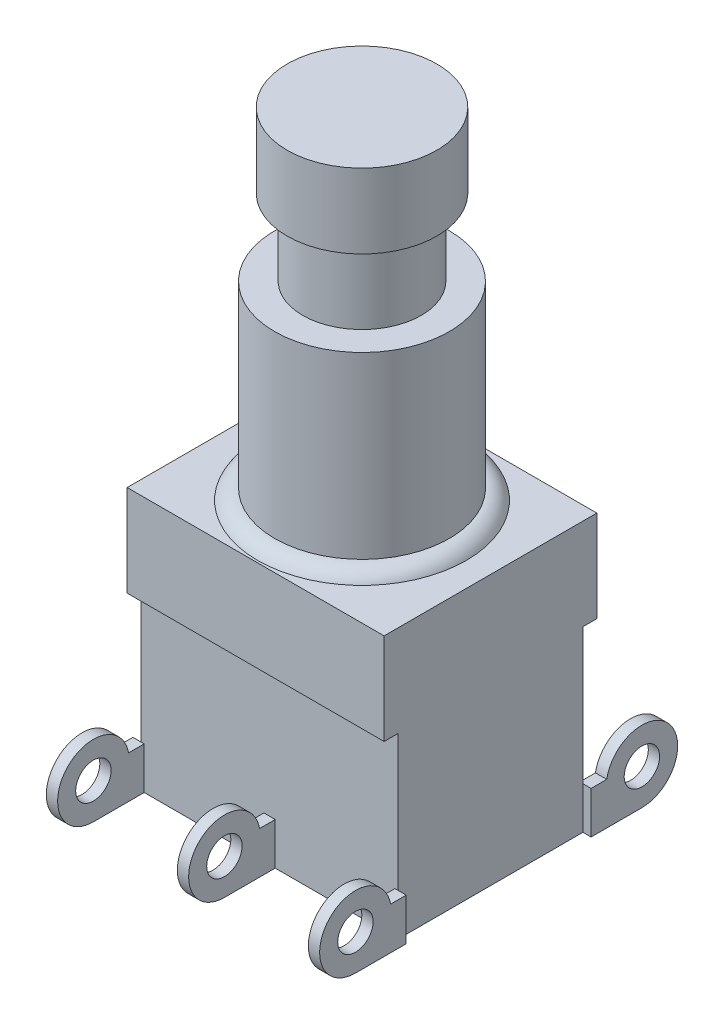
SolidWorks part; units mm, degrees
ref_plane "Front Plane" through (0, 0, 0) normal (0, 0, 1) x (1, 0, 0)
ref_plane "Top Plane" through (0, 0, 0) normal (0, 1, 0) x (1, 0, 0)
ref_plane "Right Plane" through (0, 0, 0) normal (1, 0, 0) x (0, 0, -1)
sketch "Sketch1" plane through (0, 0, 0) normal (0, 0, 1) x (1, 0, 0)
  line L0 (0, 17.3329) -> (0, -7.4822) construction
  line L1 (0, 0) -> (7.0358, 0)
  line L4 (5.8928, 0.7112) -> (5.8928, 12.8016)
  line L5 (5.8928, 12.8016) -> (4.0005, 12.8016)
  line L6 (4.0005, 12.8016) -> (4.0005, 17.9578)
  line L7 (4.0005, 17.9578) -> (5.0482, 17.9578)
  line L8 (5.0482, 17.9578) -> (5.0482, 22.9743)
  line L9 (5.0482, 22.9743) -> (0, 22.9743)
  line L10 (0, 22.9743) -> (0, 0)
  arc A0 (5.8928, 0.7112) -> (7.0358, 0) centre (5.8928, -0.5629) cw
  point P6 (0, 17.3329)
  point P10 (7.0358, 0)
  dimension "D1" = 14.0716
  dimension "D2" = 11.7856
  dimension "D3" = 8.001
  dimension "D4" = 10.0965
  dimension "D5" = 5.0165
  dimension "D6" = 5.1562
  dimension "D7" = 12.0904
  dimension "D8" = 0.7112
revolve "Revolve1" add sketch "Sketch1" angle 360 about L0
sketch "Sketch2" plane through (0, 0, 0) normal (0, -1, 0) x (1, 0, 0)
  line L1 (8.6677, -7.1755) -> (-8.6677, -7.1755)
  line L2 (8.6677, -7.1755) -> (8.6677, 7.1755)
  line L3 (8.6677, 7.1755) -> (-8.6677, 7.1755)
  line L4 (-8.6677, -7.1755) -> (-8.6677, 7.1755)
  line L5 (8.6677, -7.1755) -> (-8.6677, 7.1755) construction
  line L6 (8.6677, 7.1755) -> (-8.6677, -7.1755) construction
  point P0 (0, 0)
  dimension "D1" = 14.351
  dimension "D2" = 17.3355
extrude "Boss-Extrude1" add sketch "Sketch2" along normal blind 6.1722
sketch "Sketch3" plane through (0, -6.1722, 0) normal (0, -1, 0) x (1, 0, 0)
  line L0 (-8.6677, 7.1755) -> (-8.6677, -7.1755) construction
  line L1 (8.6678, -6.2357) -> (-8.6677, -6.2357)
  line L2 (8.6678, -6.2357) -> (8.6678, 6.2357)
  line L3 (8.6678, 6.2357) -> (-8.6677, 6.2357)
  line L4 (-8.6677, -6.2357) -> (-8.6677, 6.2357)
  line L5 (8.6678, -6.2357) -> (-8.6677, 6.2357) construction
  line L6 (8.6678, 6.2357) -> (-8.6677, -6.2357) construction
  point P0 (0, 0)
  dimension "D1" = 12.4714
extrude "Boss-Extrude2" add sketch "Sketch3" along normal blind 12.0142
sketch "Sketch4" plane through (0, 0, 0) normal (1, 0, 0) x (0, 0, -1)
  line L0 (6.2357, -18.1864) -> (6.2357, -6.1722) construction
  line L1 (6.2357, -18.1864) -> (9.6647, -18.1864)
  line L2 (6.2357, -18.1864) -> (6.2357, -15.3416)
  line L3 (6.2357, -15.3416) -> (7.2906, -15.3416)
  arc A0 (9.6647, -18.1864) -> (7.2906, -15.3416) centre (9.6647, -15.7734) ccw
  circle A1 centre (9.6647, -15.7734) radius 1.1938
  point P7 (12.0777, -15.7734)
  dimension "D1" = 2.413
  dimension "D2" = 2.3876
  dimension "D3" = 5.842
  dimension "D4" = 2.8448
extrude "Boss-Extrude3" add sketch "Sketch4" along normal mid plane 0.762
pattern_linear "LPattern1" count 2 spacing 8.8392 along (1, 0, 0) count 2 spacing 8.8392 along (-1, 0, 0) of "Boss-Extrude3"
mirror "Mirror1" about plane through (0, 0, 0) normal (0, 0, 1) of "LPattern1", "Boss-Extrude3"
